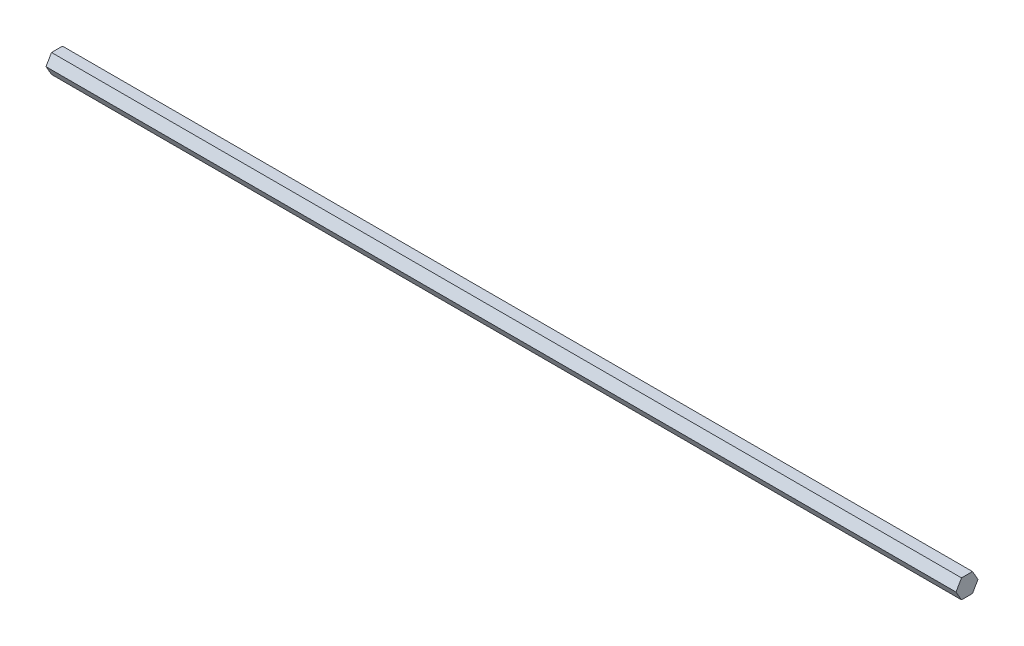
SolidWorks part; units mm, degrees
ref_plane "Front Plane" through (0, 0, 0) normal (0, 0, 1) x (1, 0, 0)
ref_plane "Top Plane" through (0, 0, 0) normal (0, 1, 0) x (1, 0, 0)
ref_plane "Right Plane" through (0, 0, 0) normal (1, 0, 0) x (0, 0, -1)
sketch "Sketch1" plane through (0, 0, 0) normal (1, 0, 0) x (0, 0, -1)
  line L1 (7.3323, 0) -> (3.6662, 6.35)
  line L2 (3.6662, 6.35) -> (-3.6662, 6.35)
  line L3 (-3.6662, 6.35) -> (-7.3323, 0)
  line L4 (-7.3323, 0) -> (-3.6662, -6.35)
  line L5 (-3.6662, -6.35) -> (3.6662, -6.35)
  line L6 (3.6662, -6.35) -> (7.3323, 0)
  circle A0 centre (0, 0) radius 6.35 construction
  dimension "D1" = 12.7
extrude "Boss-Extrude1" add sketch "Sketch1" along normal mid plane 606.425
